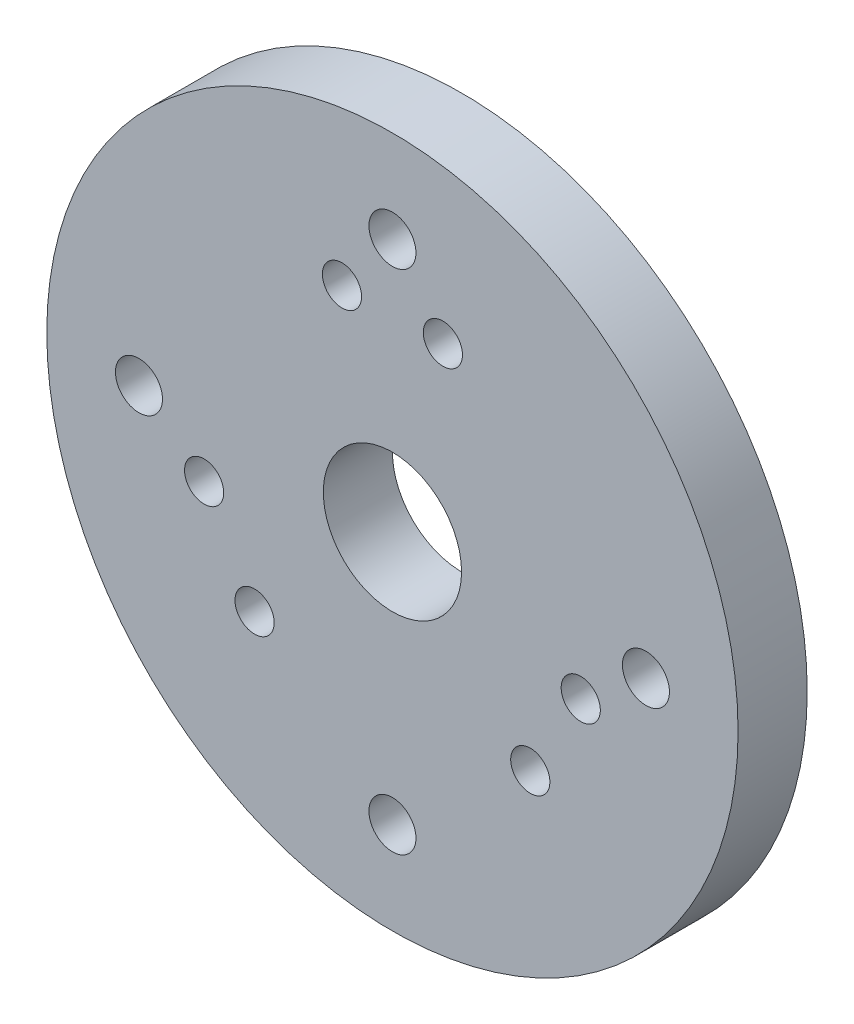
SolidWorks part; units mm, degrees
material "Acier S235"
ref_plane "Plan de face" through (0, 0, 0) normal (0, 0, 1) x (1, 0, 0)
ref_plane "Plan de dessus" through (0, 0, 0) normal (0, 1, 0) x (1, 0, 0)
ref_plane "Plan de droite" through (0, 0, 0) normal (1, 0, 0) x (0, 0, -1)
sketch "Esquisse1" plane through (0, 0, 0) normal (0, 0, 1) x (1, 0, 0)
  line L0 (0, 0) -> (-55, 0) construction
  line L1 (-55, 0) -> (0, 55) construction
  line L2 (0, -55) -> (0, 0) construction
  line L3 (0, 0) -> (55, 0) construction
  line L4 (0, 55) -> (55, 0) construction
  line L5 (0, 55) -> (0, 0) construction
  line L6 (55, 0) -> (0, -55) construction
  line L7 (0, -55) -> (-55, 0) construction
  line L8 (-10.948, 40.8587) -> (0, 0) construction
  line L9 (0, 0) -> (10.948, 40.8587) construction
  circle A0 centre (0, 0) radius 75
  circle A1 centre (0, 0) radius 55 construction
  circle A2 centre (0, 0) radius 15
  circle A3 centre (0, 55) radius 5.1
  circle A4 centre (-55, 0) radius 5.1
  circle A5 centre (0, -55) radius 5.1
  circle A6 centre (55, 0) radius 5.1
  circle A7 centre (10.948, 40.8587) radius 4.25
  circle A8 centre (0, 0) radius 42.3 construction
  circle A9 centre (-10.948, 40.8587) radius 4.25
  circle A10 centre (29.9106, -29.9106) radius 4.25
  circle A11 centre (40.8587, -10.948) radius 4.25
  circle A12 centre (-40.8587, -10.948) radius 4.25
  circle A13 centre (-29.9106, -29.9106) radius 4.25
  point P29 (0, 0)
  dimension "D1" = 30
  dimension "D2" = 110
  dimension "D3" = 150
  dimension "D4" = 10.2
  dimension "D5" = 8.5
  dimension "D6" = 84.6
  dimension "D7" = 8.5
  dimension "D9" = 30
  dimension "D8" = 3
extrude "Boss.-Extru.1" add sketch "Esquisse1" along normal mid plane 15
